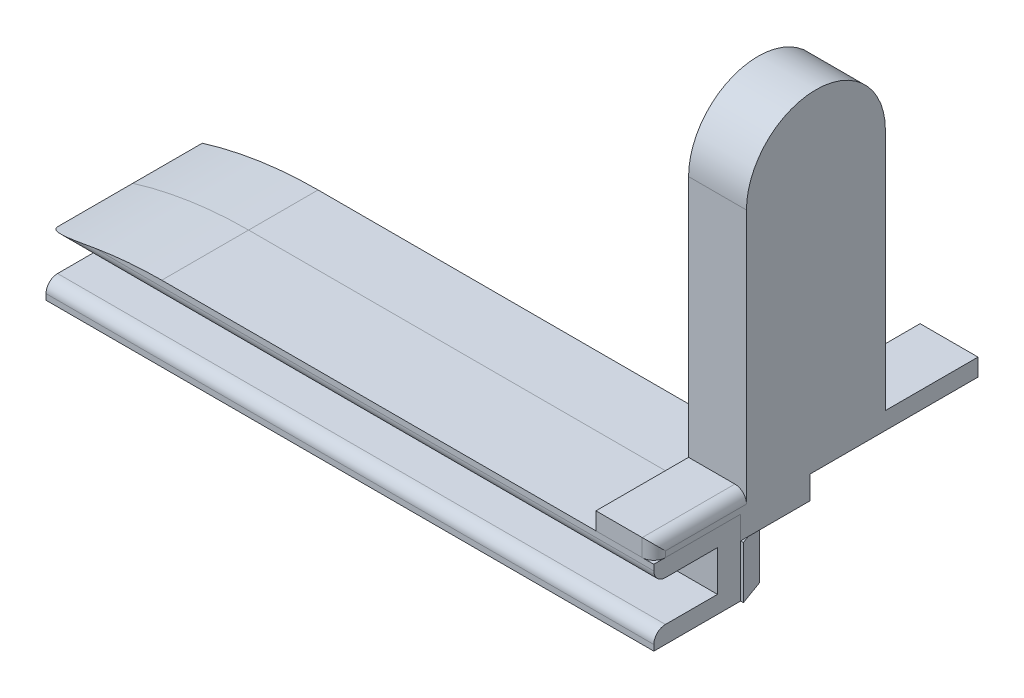
SolidWorks part; units mm, degrees
material "ABS"
ref_plane "Front Plane" through (0, 0, 0) normal (0, 0, 1) x (1, 0, 0)
ref_plane "Top Plane" through (0, 0, 0) normal (0, 1, 0) x (1, 0, 0)
ref_plane "Right Plane" through (0, 0, 0) normal (1, 0, 0) x (0, 0, -1)
sketch "Sketch1" plane through (0, 0, 0) normal (0, 1, 0) x (1, 0, 0)
  line L1 (-63.8587, 6.2481) -> (1.1413, 6.2481)
  line L2 (-63.8587, 6.2481) -> (-63.8587, 4.2481)
  line L3 (-63.8587, 4.2481) -> (1.1413, 4.2481)
  line L4 (1.1413, 6.2481) -> (1.1413, 4.2481)
  dimension "D1" = 65
  dimension "D2" = 2
extrude "Boss-Extrude1" add sketch "Sketch1" along normal blind 6.5
sketch "Sketch2" plane through (0, 0, 0) normal (0, 1, 0) x (1, 0, 0)
  line L0 (-63.8587, 6.2481) -> (-62.6387, 9.6031) construction
  line L1 (-62.6387, 9.6031) -> (-61.4187, 6.2481) construction
  line L2 (1.1413, 6.2481) -> (-63.8587, 6.2481) construction
  line L3 (-63.8587, 6.2481) -> (-61.4187, 6.2481)
  line L4 (-62.6387, 9.6031) -> (-62.6387, 6.2481) construction
  line L5 (-63.0587, 8.4481) -> (-62.2187, 8.4481)
  line L6 (-63.0587, 8.4481) -> (-63.8587, 6.2481)
  line L7 (-62.2187, 8.4481) -> (-61.4187, 6.2481)
  line L8 (-60.7187, 6.2481) -> (-58.2787, 6.2481)
  line L9 (-59.9187, 8.4481) -> (-60.7187, 6.2481)
  line L10 (-59.0787, 8.4481) -> (-58.2787, 6.2481)
  line L11 (-60.7187, 6.2481) -> (-59.4987, 9.6031) construction
  line L12 (-59.4987, 9.6031) -> (-58.2787, 6.2481) construction
  line L13 (-59.4987, 9.6031) -> (-59.4987, 6.2481) construction
  line L14 (-59.9187, 8.4481) -> (-59.0787, 8.4481)
  line L15 (-57.5787, 6.2481) -> (-55.1387, 6.2481)
  line L16 (-56.7787, 8.4481) -> (-57.5787, 6.2481)
  line L17 (-55.9387, 8.4481) -> (-55.1387, 6.2481)
  line L18 (-57.5787, 6.2481) -> (-56.3587, 9.6031) construction
  line L19 (-56.3587, 9.6031) -> (-55.1387, 6.2481) construction
  line L20 (-56.3587, 9.6031) -> (-56.3587, 6.2481) construction
  line L21 (-56.7787, 8.4481) -> (-55.9387, 8.4481)
  line L22 (-54.4387, 6.2481) -> (-51.9987, 6.2481)
  line L23 (-53.6387, 8.4481) -> (-54.4387, 6.2481)
  line L24 (-52.7987, 8.4481) -> (-51.9987, 6.2481)
  line L25 (-54.4387, 6.2481) -> (-53.2187, 9.6031) construction
  line L26 (-53.2187, 9.6031) -> (-51.9987, 6.2481) construction
  line L27 (-53.2187, 9.6031) -> (-53.2187, 6.2481) construction
  line L28 (-53.6387, 8.4481) -> (-52.7987, 8.4481)
  line L29 (-51.2987, 6.2481) -> (-48.8587, 6.2481)
  line L30 (-50.4987, 8.4481) -> (-51.2987, 6.2481)
  line L31 (-49.6587, 8.4481) -> (-48.8587, 6.2481)
  line L32 (-51.2987, 6.2481) -> (-50.0787, 9.6031) construction
  line L33 (-50.0787, 9.6031) -> (-48.8587, 6.2481) construction
  line L34 (-50.0787, 9.6031) -> (-50.0787, 6.2481) construction
  line L35 (-50.4987, 8.4481) -> (-49.6587, 8.4481)
  line L36 (-48.1587, 6.2481) -> (-45.7187, 6.2481)
  line L37 (-47.3587, 8.4481) -> (-48.1587, 6.2481)
  line L38 (-46.5187, 8.4481) -> (-45.7187, 6.2481)
  line L39 (-48.1587, 6.2481) -> (-46.9387, 9.6031) construction
  line L40 (-46.9387, 9.6031) -> (-45.7187, 6.2481) construction
  line L41 (-46.9387, 9.6031) -> (-46.9387, 6.2481) construction
  line L42 (-47.3587, 8.4481) -> (-46.5187, 8.4481)
  line L43 (-45.0187, 6.2481) -> (-42.5787, 6.2481)
  line L44 (-44.2187, 8.4481) -> (-45.0187, 6.2481)
  line L45 (-43.3787, 8.4481) -> (-42.5787, 6.2481)
  line L46 (-45.0187, 6.2481) -> (-43.7987, 9.6031) construction
  line L47 (-43.7987, 9.6031) -> (-42.5787, 6.2481) construction
  line L48 (-43.7987, 9.6031) -> (-43.7987, 6.2481) construction
  line L49 (-44.2187, 8.4481) -> (-43.3787, 8.4481)
  line L50 (-41.8787, 6.2481) -> (-39.4387, 6.2481)
  line L51 (-41.0787, 8.4481) -> (-41.8787, 6.2481)
  line L52 (-40.2387, 8.4481) -> (-39.4387, 6.2481)
  line L53 (-41.8787, 6.2481) -> (-40.6587, 9.6031) construction
  line L54 (-40.6587, 9.6031) -> (-39.4387, 6.2481) construction
  line L55 (-40.6587, 9.6031) -> (-40.6587, 6.2481) construction
  line L56 (-41.0787, 8.4481) -> (-40.2387, 8.4481)
  line L57 (-38.7387, 6.2481) -> (-36.2987, 6.2481)
  line L58 (-37.9387, 8.4481) -> (-38.7387, 6.2481)
  line L59 (-37.0987, 8.4481) -> (-36.2987, 6.2481)
  line L60 (-38.7387, 6.2481) -> (-37.5187, 9.6031) construction
  line L61 (-37.5187, 9.6031) -> (-36.2987, 6.2481) construction
  line L62 (-37.5187, 9.6031) -> (-37.5187, 6.2481) construction
  line L63 (-37.9387, 8.4481) -> (-37.0987, 8.4481)
  line L64 (-35.5987, 6.2481) -> (-33.1587, 6.2481)
  line L65 (-34.7987, 8.4481) -> (-35.5987, 6.2481)
  line L66 (-33.9587, 8.4481) -> (-33.1587, 6.2481)
  line L67 (-35.5987, 6.2481) -> (-34.3787, 9.6031) construction
  line L68 (-34.3787, 9.6031) -> (-33.1587, 6.2481) construction
  line L69 (-34.3787, 9.6031) -> (-34.3787, 6.2481) construction
  line L70 (-34.7987, 8.4481) -> (-33.9587, 8.4481)
  line L71 (-32.4587, 6.2481) -> (-30.0187, 6.2481)
  line L72 (-31.6587, 8.4481) -> (-32.4587, 6.2481)
  line L73 (-30.8187, 8.4481) -> (-30.0187, 6.2481)
  line L74 (-32.4587, 6.2481) -> (-31.2387, 9.6031) construction
  line L75 (-31.2387, 9.6031) -> (-30.0187, 6.2481) construction
  line L76 (-31.2387, 9.6031) -> (-31.2387, 6.2481) construction
  line L77 (-31.6587, 8.4481) -> (-30.8187, 8.4481)
  line L78 (-29.3187, 6.2481) -> (-26.8787, 6.2481)
  line L79 (-28.5187, 8.4481) -> (-29.3187, 6.2481)
  line L80 (-27.6787, 8.4481) -> (-26.8787, 6.2481)
  line L81 (-29.3187, 6.2481) -> (-28.0987, 9.6031) construction
  line L82 (-28.0987, 9.6031) -> (-26.8787, 6.2481) construction
  line L83 (-28.0987, 9.6031) -> (-28.0987, 6.2481) construction
  line L84 (-28.5187, 8.4481) -> (-27.6787, 8.4481)
  line L85 (-26.1787, 6.2481) -> (-23.7387, 6.2481)
  line L86 (-25.3787, 8.4481) -> (-26.1787, 6.2481)
  line L87 (-24.5387, 8.4481) -> (-23.7387, 6.2481)
  line L88 (-26.1787, 6.2481) -> (-24.9587, 9.6031) construction
  line L89 (-24.9587, 9.6031) -> (-23.7387, 6.2481) construction
  line L90 (-24.9587, 9.6031) -> (-24.9587, 6.2481) construction
  line L91 (-25.3787, 8.4481) -> (-24.5387, 8.4481)
  line L92 (-23.0387, 6.2481) -> (-20.5987, 6.2481)
  line L93 (-22.2387, 8.4481) -> (-23.0387, 6.2481)
  line L94 (-21.3987, 8.4481) -> (-20.5987, 6.2481)
  line L95 (-23.0387, 6.2481) -> (-21.8187, 9.6031) construction
  line L96 (-21.8187, 9.6031) -> (-20.5987, 6.2481) construction
  line L97 (-21.8187, 9.6031) -> (-21.8187, 6.2481) construction
  line L98 (-22.2387, 8.4481) -> (-21.3987, 8.4481)
  line L99 (-19.8987, 6.2481) -> (-17.4587, 6.2481)
  line L100 (-19.0987, 8.4481) -> (-19.8987, 6.2481)
  line L101 (-18.2587, 8.4481) -> (-17.4587, 6.2481)
  line L102 (-19.8987, 6.2481) -> (-18.6787, 9.6031) construction
  line L103 (-18.6787, 9.6031) -> (-17.4587, 6.2481) construction
  line L104 (-18.6787, 9.6031) -> (-18.6787, 6.2481) construction
  line L105 (-19.0987, 8.4481) -> (-18.2587, 8.4481)
  line L106 (-16.7587, 6.2481) -> (-14.3187, 6.2481)
  line L107 (-15.9587, 8.4481) -> (-16.7587, 6.2481)
  line L108 (-15.1187, 8.4481) -> (-14.3187, 6.2481)
  line L109 (-16.7587, 6.2481) -> (-15.5387, 9.6031) construction
  line L110 (-15.5387, 9.6031) -> (-14.3187, 6.2481) construction
  line L111 (-15.5387, 9.6031) -> (-15.5387, 6.2481) construction
  line L112 (-15.9587, 8.4481) -> (-15.1187, 8.4481)
  line L113 (-13.6187, 6.2481) -> (-11.1787, 6.2481)
  line L114 (-12.8187, 8.4481) -> (-13.6187, 6.2481)
  line L115 (-11.9787, 8.4481) -> (-11.1787, 6.2481)
  line L116 (-13.6187, 6.2481) -> (-12.3987, 9.6031) construction
  line L117 (-12.3987, 9.6031) -> (-11.1787, 6.2481) construction
  line L118 (-12.3987, 9.6031) -> (-12.3987, 6.2481) construction
  line L119 (-12.8187, 8.4481) -> (-11.9787, 8.4481)
  line L120 (-10.4787, 6.2481) -> (-8.0387, 6.2481)
  line L121 (-9.6787, 8.4481) -> (-10.4787, 6.2481)
  line L122 (-8.8387, 8.4481) -> (-8.0387, 6.2481)
  line L123 (-10.4787, 6.2481) -> (-9.2587, 9.6031) construction
  line L124 (-9.2587, 9.6031) -> (-8.0387, 6.2481) construction
  line L125 (-9.2587, 9.6031) -> (-9.2587, 6.2481) construction
  line L126 (-9.6787, 8.4481) -> (-8.8387, 8.4481)
  line L127 (-7.3387, 6.2481) -> (-4.8987, 6.2481)
  line L128 (-6.5387, 8.4481) -> (-7.3387, 6.2481)
  line L129 (-5.6987, 8.4481) -> (-4.8987, 6.2481)
  line L130 (-7.3387, 6.2481) -> (-6.1187, 9.6031) construction
  line L131 (-6.1187, 9.6031) -> (-4.8987, 6.2481) construction
  line L132 (-6.1187, 9.6031) -> (-6.1187, 6.2481) construction
  line L133 (-6.5387, 8.4481) -> (-5.6987, 8.4481)
  line L134 (-4.1987, 6.2481) -> (-1.7587, 6.2481)
  line L135 (-3.3987, 8.4481) -> (-4.1987, 6.2481)
  line L136 (-2.5587, 8.4481) -> (-1.7587, 6.2481)
  line L137 (-4.1987, 6.2481) -> (-2.9787, 9.6031) construction
  line L138 (-2.9787, 9.6031) -> (-1.7587, 6.2481) construction
  line L139 (-2.9787, 9.6031) -> (-2.9787, 6.2481) construction
  line L140 (-3.3987, 8.4481) -> (-2.5587, 8.4481)
  line L141 (-1.0587, 6.2481) -> (1.3813, 6.2481)
  line L142 (-0.2587, 8.4481) -> (-1.0587, 6.2481)
  line L143 (0.5813, 8.4481) -> (1.3813, 6.2481)
  line L144 (-1.0587, 6.2481) -> (0.1613, 9.6031) construction
  line L145 (0.1613, 9.6031) -> (1.3813, 6.2481) construction
  line L146 (0.1613, 9.6031) -> (0.1613, 6.2481) construction
  line L147 (-0.2587, 8.4481) -> (0.5813, 8.4481)
  line L148 (2.0813, 6.2481) -> (4.5213, 6.2481)
  line L149 (2.8813, 8.4481) -> (2.0813, 6.2481)
  line L150 (3.7213, 8.4481) -> (4.5213, 6.2481)
  line L151 (2.0813, 6.2481) -> (3.3013, 9.6031) construction
  line L152 (3.3013, 9.6031) -> (4.5213, 6.2481) construction
  line L153 (3.3013, 9.6031) -> (3.3013, 6.2481) construction
  line L154 (2.8813, 8.4481) -> (3.7213, 8.4481)
  line L155 (5.2213, 6.2481) -> (7.6613, 6.2481)
  line L156 (6.0213, 8.4481) -> (5.2213, 6.2481)
  line L157 (6.8613, 8.4481) -> (7.6613, 6.2481)
  line L158 (5.2213, 6.2481) -> (6.4413, 9.6031) construction
  line L159 (6.4413, 9.6031) -> (7.6613, 6.2481) construction
  line L160 (6.4413, 9.6031) -> (6.4413, 6.2481) construction
  line L161 (6.0213, 8.4481) -> (6.8613, 8.4481)
  dimension "D1" = 2.44
  dimension "D2" = 2.2
  dimension "D3" = 0.84
  dimension "D5" = 0.7
  dimension "D4" = 23
extrude "Boss-Extrude2" add sketch "Sketch2" along normal blind 4.5
sketch "Sketch5" plane through (0, 0, -4.2481) normal (0, 0, 1) x (1, 0, 0)
  line L0 (-65.8587, 15) -> (-65.8587, 0) construction
  line L1 (-65.8587, 0) -> (1.1413, 0)
  line L2 (-65.8587, 0) -> (-65.8587, 1.5)
  line L3 (-65.8587, 1.5) -> (1.1413, 1.5)
  line L4 (1.1413, 0) -> (1.1413, 1.5)
  line L5 (1.1413, 6.5) -> (-65.8587, 6.5)
  line L6 (1.1413, 6.5) -> (1.1413, 5)
  line L7 (1.1413, 5) -> (-65.8587, 5)
  line L8 (-65.8587, 6.5) -> (-65.8587, 5)
  line L9 (1.1413, 6.5) -> (1.1413, 0) construction
  line L11 (-63.8587, 6.5) -> (1.1413, 6.5) construction
  dimension "D1" = 1.5
extrude "Boss-Extrude6" add sketch "Sketch5" along normal blind 5.5
sketch "Sketch6" plane through (1.1413, 0, 0) normal (1, 0, 0) x (0, 0, -1)
  line L0 (6.2481, 6.5) -> (26.7481, 6.5)
  line L1 (6.2481, 6.5) -> (-1.2519, 6.5)
  line L2 (6.7481, 8) -> (6.7481, 29)
  line L3 (18.7481, 8) -> (18.7481, 29)
  line L4 (12.7481, 35) -> (12.7481, 6.5) construction
  line L5 (18.7481, 8) -> (6.7481, 8) construction
  line L6 (26.7481, 6.5) -> (26.7481, 8)
  line L7 (-1.2519, 6.5) -> (-1.2519, 8)
  line L8 (-1.2519, 8) -> (6.7481, 8)
  line L9 (26.7481, 8) -> (18.7481, 8)
  arc A2 (6.7481, 29) -> (18.7481, 29) centre (12.7481, 29) cw
  dimension "D1" = 12
  dimension "D2" = 27
  dimension "D3" = 1.5
  dimension "D4" = 28
extrude "Boss-Extrude7" add sketch "Sketch6" against normal blind 5 separate body
sketch "Sketch7" plane through (0, 0, -6.2481) normal (0, 0, -1) x (-1, 0, 0)
  line L0 (63.8587, 4.5) -> (63.8587, 0) construction
  line L1 (-1.1413, 6.5) -> (63.8587, 6.5)
  line L2 (-1.1413, 6.5) -> (-1.1413, 4.5)
  line L3 (-1.1413, 4.5) -> (63.8587, 4.5)
  line L4 (63.8587, 6.5) -> (63.8587, 4.5)
  dimension "D1" = 2
extrude "Boss-Extrude8" add sketch "Sketch7" along normal blind 6
sketch "Sketch8" plane through (0, 0, 0) normal (0, -1, 0) x (-1, 0, 0)
  line L1 (51.3588, 19.949) -> (76.6817, 19.949)
  line L2 (51.3588, 19.949) -> (51.3588, -9.1419)
  line L3 (51.3588, -9.1419) -> (76.6817, -9.1419)
  line L4 (76.6817, 19.949) -> (76.6817, -9.1419)
extrude "Cut-Extrude1" cut sketch "Sketch8" against normal through all
sketch "Sketch10" plane through (0, 0, 1.2519) normal (0, 0, 1) x (1, 0, 0)
  line L0 (1.1413, 6.5) -> (-51.3588, 6.5) construction
  line L1 (-51.3588, 5) -> (-51.3588, 6.5)
  line L2 (-51.3588, 6.5) -> (-41.3588, 6.5)
  arc A0 (-41.3588, 6.5) -> (-51.3588, 5) centre (-41.3588, -27.5833) ccw
  line M1 (1.1413, 6.5) -> (-51.3588, 6.5)
  line M2 (-51.3588, 6.5) -> (-51.3588, 5)
  dimension "D1" = 10
extrude "Cut-Extrude2" cut sketch "Sketch10" along direction (0, 0, -1) on the side against the normal through all contours A0 M1 M2
fillet "Fillet5" radius 1 2 edges at (1.1413, 7.25, 1.2519) (1.1413, 8, -2.7481)
fillet "Fillet7" radius 1 2 edges at (-25.1087, 5, 1.2519) (-25.1087, 1.5, 1.2519)
